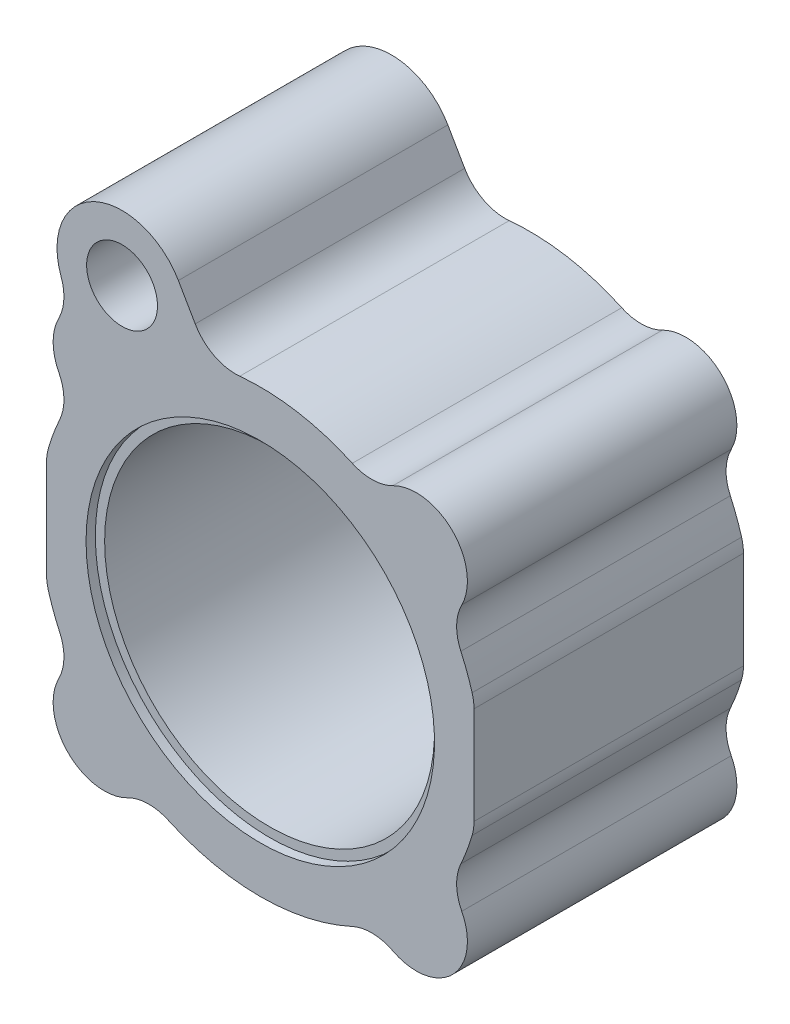
SolidWorks part; units mm, degrees
ref_plane "Front" through (0, 0, 0) normal (0, 0, 1) x (1, 0, 0)
ref_plane "Top" through (0, 0, 0) normal (0, 1, 0) x (1, 0, 0)
ref_plane "Right" through (0, 0, 0) normal (1, 0, 0) x (0, 0, -1)
sketch "Sketch1" plane through (0, 0, 0) normal (0, 0, 1) x (1, 0, 0)
  line L0 (-78.8178, 0) -> (107.0564, 0) construction
  line L1 (0, 98.2988) -> (0, -103.3031) construction
  line L2 (0, 0) -> (73.9042, 73.9042) construction
  line L3 (46, 10.5) -> (46, -10.5)
  line L4 (-46, 10.5) -> (-46, -10.5)
  line L5 (0, 0) -> (-44.2409, 76.6275) construction
  line L6 (-46, 0) -> (-46, 65.7651) construction
  line L7 (-17.6256, 58.5285) -> (-14.0015, 52.2514)
  line L9 (46, 0) -> (46, 70.617) construction
  arc A0 (19.8096, 43.1721) -> (0, 47.5) centre (0, 0) ccw
  circle A1 centre (0, 0) radius 47.5 construction
  arc A2 (43.3689, 28.5551) -> (28.5551, 43.3689) centre (33.5876, 33.5876) ccw
  arc A3 (45.6, 13.3) -> (43.1721, 19.8096) centre (0, 0) ccw
  arc A4 (28.5551, 43.3689) -> (19.8096, 43.1721) centre (23.98, 52.261) cw
  arc A5 (43.1721, 19.8096) -> (43.3689, 28.5551) centre (52.261, 23.98) cw
  arc A6 (46, 10.5) -> (45.6, 13.3) centre (36, 10.5) ccw
  arc A7 (46, -10.5) -> (45.6, -13.3) centre (36, -10.5) cw
  arc A8 (43.1721, -19.8096) -> (43.3689, -28.5551) centre (52.261, -23.98) ccw
  arc A9 (28.5551, -43.3689) -> (19.8096, -43.1721) centre (23.98, -52.261) ccw
  arc A10 (45.6, -13.3) -> (43.1721, -19.8096) centre (0, 0) cw
  arc A11 (43.3689, -28.5551) -> (28.5551, -43.3689) centre (33.5876, -33.5876) cw
  arc A12 (19.8096, -43.1721) -> (-19.8096, -43.1721) centre (0, 0) cw
  arc A13 (-43.3689, -28.5551) -> (-28.5551, -43.3689) centre (-33.5876, -33.5876) ccw
  arc A14 (-45.6, -13.3) -> (-43.1721, -19.8096) centre (0, 0) ccw
  arc A15 (-28.5551, -43.3689) -> (-19.8096, -43.1721) centre (-23.98, -52.261) cw
  arc A16 (-43.1721, -19.8096) -> (-43.3689, -28.5551) centre (-52.261, -23.98) cw
  arc A17 (-46, -10.5) -> (-45.6, -13.3) centre (-36, -10.5) ccw
  arc A18 (-46, 10.5) -> (-45.6, 13.3) centre (-36, 10.5) cw
  arc A19 (-43.1721, 19.8096) -> (-43.3689, 28.5551) centre (-52.261, 23.98) ccw
  arc A20 (-14.0015, 52.2514) -> (-4.4124, 47.2946) centre (-5.3413, 57.2514) ccw
  arc A21 (-45.6, 13.3) -> (-43.1721, 19.8096) centre (0, 0) cw
  arc A22 (-43.3689, 28.5551) -> (-43.3676, 38.6226) centre (-33.5876, 33.5876) cw
  arc A23 (0, 47.5) -> (-4.4124, 47.2946) centre (0, 0) ccw
  arc A24 (-42.88, 46.6701) -> (-43.3676, 38.6226) centre (-52.2585, 43.1998) cw
  arc A25 (-17.6256, 58.5285) -> (-42.88, 46.6701) centre (-29.75, 51.5285) ccw
  circle A26 centre (0, 0) radius 31.5
  point P31 (46, 0)
  point P50 (-46, 0)
  dimension "D2" = 95
  dimension "D3" = 11
  dimension "D6" = 10
  dimension "D7" = 10
  dimension "D8" = 10
  dimension "D12" = 10
  dimension "D13" = 10
  dimension "D14" = 2.25
  dimension "D15" = 1.4124
  dimension "D10" = 14
  dimension "D16" = 63
  dimension "D4" = 45
  dimension "D5" = 92
  dimension "D9" = 30
  dimension "D11" = 59.5
extrude "Base-Extrude" add sketch "Sketch1" along normal blind 60
sketch "Sketch2" plane through (0, 0, 0) normal (1, 0, 0) x (0, 0, -1)
  line L0 (0, 0) -> (-117.4351, 0) construction
  line L1 (-60, 0) -> (0, 0) construction
  line L2 (0, 10.5) -> (0, -10.5) construction
  line L3 (0, 90) -> (0, 0)
  line L4 (-60, 10.5) -> (-60, -10.5) construction
  line L5 (-60, 90) -> (-60, 0)
  line L6 (0, 90) -> (-1, 90)
  line L8 (-59, 37.5) -> (-59, 90)
  line L9 (-59, 90) -> (-60, 90)
  line L10 (-59, 37.5) -> (-57, 37.5)
  line L11 (-57, 37.5) -> (-57, 35.5)
  line L12 (-57, 35.5) -> (-2.7321, 35.5)
  line L15 (-2.7321, 35.5) -> (-1, 36.5)
  line L18 (-1, 90) -> (-1, 36.5)
  line L19 (-2.723, 0) -> (0, 0)
  line L20 (-60, 0) -> (-2.723, 0)
  dimension "D1" = 90
  dimension "D2" = 1
  dimension "D3" = 1
  dimension "D4" = 75
  dimension "D5" = 71
  dimension "D6" = 30
  dimension "D9" = 73
  dimension "D10" = 58
  dimension "D11" = 2
revolve "Indv uddrejning" cut sketch "Sketch2" angle 360 about L0
hole_wizard "4 stk M14" positions "Sketch8" profile "Sketch7" legacy
sketch "Sketch8" plane through (0, 0, 1) normal (0, 0, -1) x (-1, 0, 0)
  line L0 (0, 0) -> (-33.5876, 33.5876) construction
  line L1 (0, 0) -> (0, 47.5) construction
  arc A0 (-28.5551, 43.3689) -> (-43.3689, 28.5551) centre (-33.5876, 33.5876) ccw construction
  arc A1 (43.3689, 28.5551) -> (43.3676, 38.6226) centre (33.5876, 33.5876) ccw construction
  arc A2 (28.5551, -43.3689) -> (43.3689, -28.5551) centre (33.5876, -33.5876) ccw construction
  arc A3 (-43.3689, -28.5551) -> (-28.5551, -43.3689) centre (-33.5876, -33.5876) ccw construction
  circle A6 centre (0, 0) radius 47.5 construction
  point P0 (-33.5876, 33.5876)
  point P2 (33.5876, 33.5876)
  point P3 (-33.5876, -33.5876)
  point P4 (33.5876, -33.5876)
  dimension "D1" = 95
  dimension "D2" = 45
sketch "Sketch7" plane through (33.5876, 33.5876, 1) normal (1, 0, 0) x (0, 1, 0)
  line L0 (0, 0) -> (0, 31.6052)
  line L1 (0, 31.6052) -> (6, 28)
  line L2 (6, 28) -> (6, 0)
  line L4 (6, 0) -> (0, 0)
  line L6 (0, 31.6052) -> (-6, 28) construction
  line L7 (0, -4.2442) -> (0, 117.3081) construction
  dimension "Diameter" = 12
  dimension "Depth" = 28
  dimension "Drill Angle" = 118
cosmetic thread "Cosmetic Thread1" parameters "D1"=23, "D2"=14
cosmetic thread "Cosmetic Thread2" parameters "D1"=23, "D2"=14
cosmetic thread "Cosmetic Thread3" parameters "D1"=23, "D2"=14
cosmetic thread "Cosmetic Thread4" parameters "D1"=23, "D2"=14
hole_wizard "3/8\" RG oliehul" positions "Sketch10" profile "Sketch9" legacy
sketch "Sketch10" plane through (0, 0, 59) normal (0, 0, 1) x (1, 0, 0)
  line L0 (0, 0) -> (-37.75, 65.3849) construction
  arc A0 (-17.6256, 58.5285) -> (-42.88, 46.6701) centre (-29.75, 51.5285) ccw construction
  point P0 (-29.75, 51.5285)
  dimension "D1" = 59.5
sketch "Sketch9" plane through (-29.75, 51.5285, 59) normal (1, 0, 0) x (0, -1, 0)
  line L0 (0, 0) -> (0, 31.5816)
  line L1 (0, 31.5816) -> (7.625, 27)
  line L2 (7.625, 27) -> (7.625, 0)
  line L4 (7.625, 0) -> (0, 0)
  line L6 (0, 31.5816) -> (-7.625, 27) construction
  line L7 (0, -4.2442) -> (0, 117.3081) construction
  dimension "Diameter" = 15.25
  dimension "Depth" = 27
  dimension "Drill Angle" = 118
cosmetic thread "Cosmetic Thread5" parameters "D1"=15, "D2"=16.662
ref_plane "Hjælpeplan - ø12 olietilførsel" through (0, 0, 0) normal (0.866, 0.5, 0) x (0, 0, -1)
sketch "Sketch11" plane through (0, 0, 0) normal (0.866, 0.5, 0) x (0, 0, -1)
  line L0 (-34.8086, 59.5) -> (-82.6889, -43.1796) construction
  line L1 (-34.8086, 59.5) -> (-30.8944, 53.6969)
  line L2 (-30.8944, 53.6969) -> (-81.6086, -55.06)
  line L3 (-81.6086, -55.06) -> (-87.0464, -52.5243)
  line L4 (0, 0) -> (-123.2382, 0) construction
  line L7 (-27.4184, 59.5) -> (-87.5641, 59.5) construction
  line L8 (-59, 52.2518) -> (-59, 59.5) construction
  line L10 (-34.8086, 59.5) -> (-87.0464, -52.5243)
  line L16 (-59, 38.7417) -> (-59, 34.3181) construction
  line L17 (-30.8944, 53.6969) -> (-36.3322, 56.2326) construction
  line L20 (-2.7321, 35.5) -> (-57, 35.5) construction
  point P13 (-46, 35.5)
  dimension "D1" = 59
  dimension "D2" = 12
  dimension "D3" = 65
  dimension "D4" = 24.1914
  dimension "D5" = 120
  dimension "D6" = 13
  dimension "D7" = 22.8759
revolve "ø12 olietilførsel" cut sketch "Sketch11" angle 360 about L0
sketch "Sketch12" plane through (0, 0, 59) normal (0, 0, 1) x (1, 0, 0)
  line L0 (-29.75, 51.5285) -> (-22.9407, 39.7345)
  line L1 (-22.9407, 39.7345) -> (-33.5876, 33.5876)
  line L2 (-33.5876, 33.5876) -> (-57.0141, 33.5876)
  line L3 (-57.0141, 33.5876) -> (-57.0141, 77.67)
  line L4 (-57.0141, 77.67) -> (-29.75, 77.67)
  line L5 (-29.75, 77.67) -> (-29.75, 51.5285)
  line L6 (-12.2985, 33.3016) -> (-22.2012, 50.4535) construction
extrude "Dummy-cut ved oliehul" [suppressed] cut sketch "Sketch12" against normal through all
